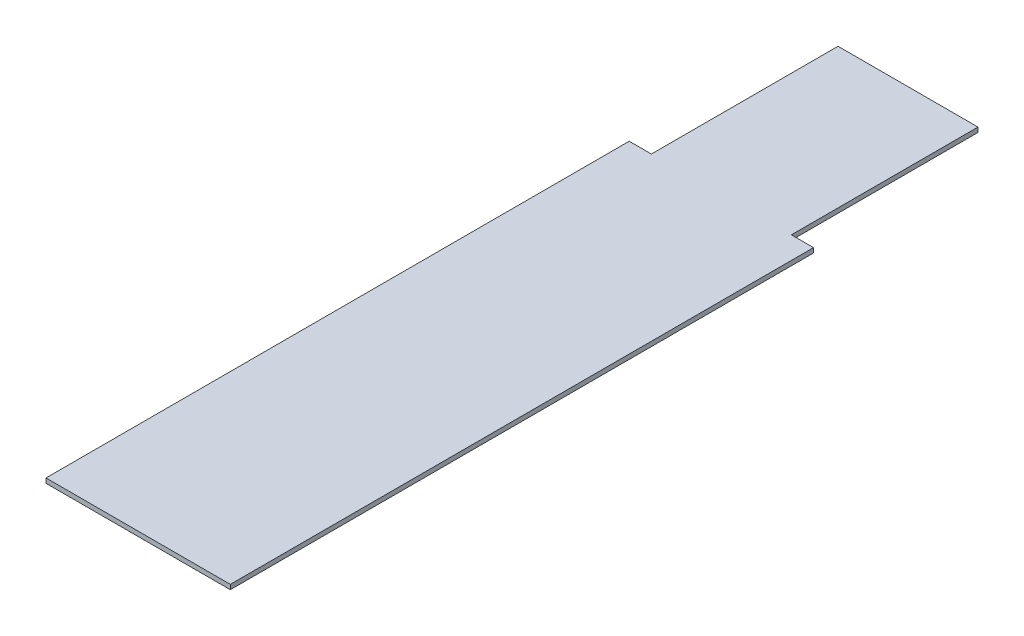
SolidWorks part; units mm, degrees
ref_plane "Ebene vorne" through (0, 0, 0) normal (0, 0, 1) x (1, 0, 0)
ref_plane "Ebene oben" through (0, 0, 0) normal (0, 1, 0) x (1, 0, 0)
ref_plane "Ebene rechts" through (0, 0, 0) normal (1, 0, 0) x (0, 0, -1)
sketch "Skizze1" plane through (0, 0, 0) normal (0, 1, 0) x (1, 0, 0)
  line L0 (-3, 12.5) -> (-3.95, 12.5)
  line L1 (3.95, -12.5) -> (-3.95, -12.5)
  line L2 (3.95, -12.5) -> (3.95, 12.5)
  line L3 (3.95, 12.5) -> (3, 12.5)
  line L4 (-3.95, -12.5) -> (-3.95, 12.5)
  line L5 (3.95, -12.5) -> (-3.95, 12.5) construction
  line L6 (3.95, 12.5) -> (-3.95, -12.5) construction
  line L7 (3, 20.5) -> (-3, 20.5)
  line L8 (3, 20.5) -> (3, 12.5)
  line L10 (-3, 20.5) -> (-3, 12.5)
  line L11 (3, 20.5) -> (-3, 12.5) construction
  line L12 (3, 12.5) -> (-3, 20.5) construction
  point P0 (0, 0)
  point P5 (0, 16.5)
  dimension "D1" = 8
  dimension "D2" = 33
  dimension "D3" = 6
  dimension "D4" = 7.9
extrude "Aufsatz-Linear austragen1" add sketch "Skizze1" along normal blind 0.2
